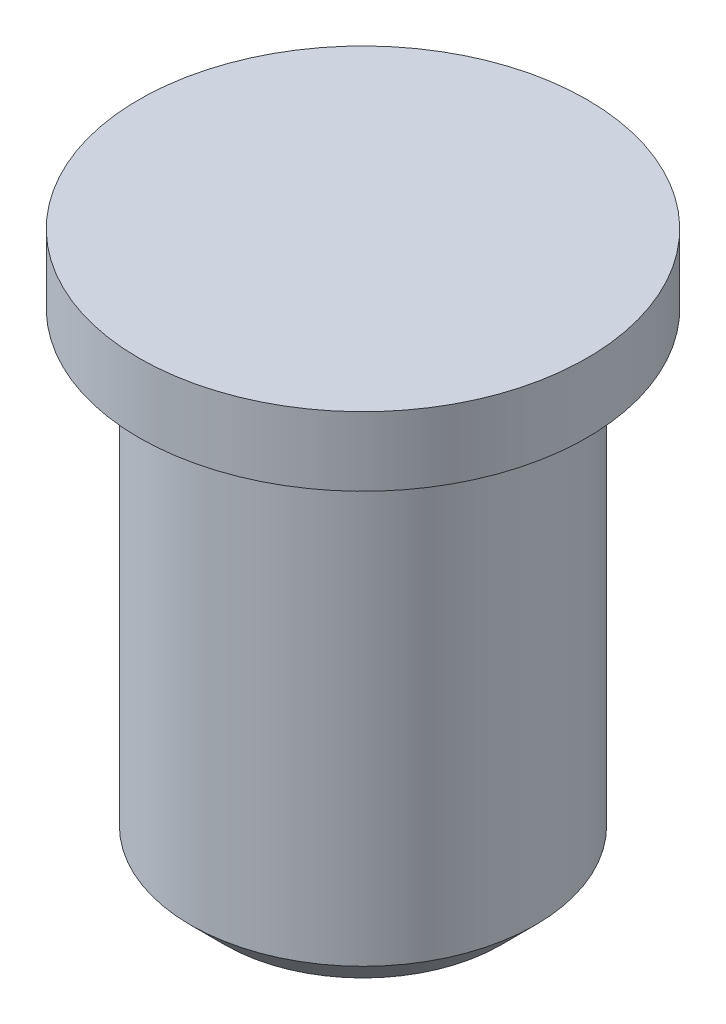
SolidWorks part; units mm, degrees
material "acero"
ref_plane "Alzado" through (0, 0, 0) normal (0, 0, 1) x (1, 0, 0)
ref_plane "Planta" through (0, 0, 0) normal (0, 1, 0) x (1, 0, 0)
ref_plane "Vista lateral" through (0, 0, 0) normal (1, 0, 0) x (0, 0, -1)
sketch "Croquis1" plane through (0, 0, 0) normal (0, 0, 1) x (1, 0, 0)
  line L0 (0, 0) -> (0, -60.9498) construction
  line L1 (0, 0) -> (3.25, 0)
  line L2 (3.25, 0) -> (3.25, -1)
  line L3 (3.25, -1) -> (2.5, -1)
  line L4 (2.5, -1) -> (2.5, -8)
  line L5 (2.5, -8) -> (0, -8)
  line L6 (0, -8) -> (0, 0)
  dimension "D1" = 8
  dimension "D2" = 1
  dimension "D3" = 6.5
  dimension "D4" = 5
revolve "Revolución1" add sketch "Croquis1" angle 360 about L0
chamfer "Chaflán1" distance 0.5 angle 45 1 edges at (0, -8, 2.5)
